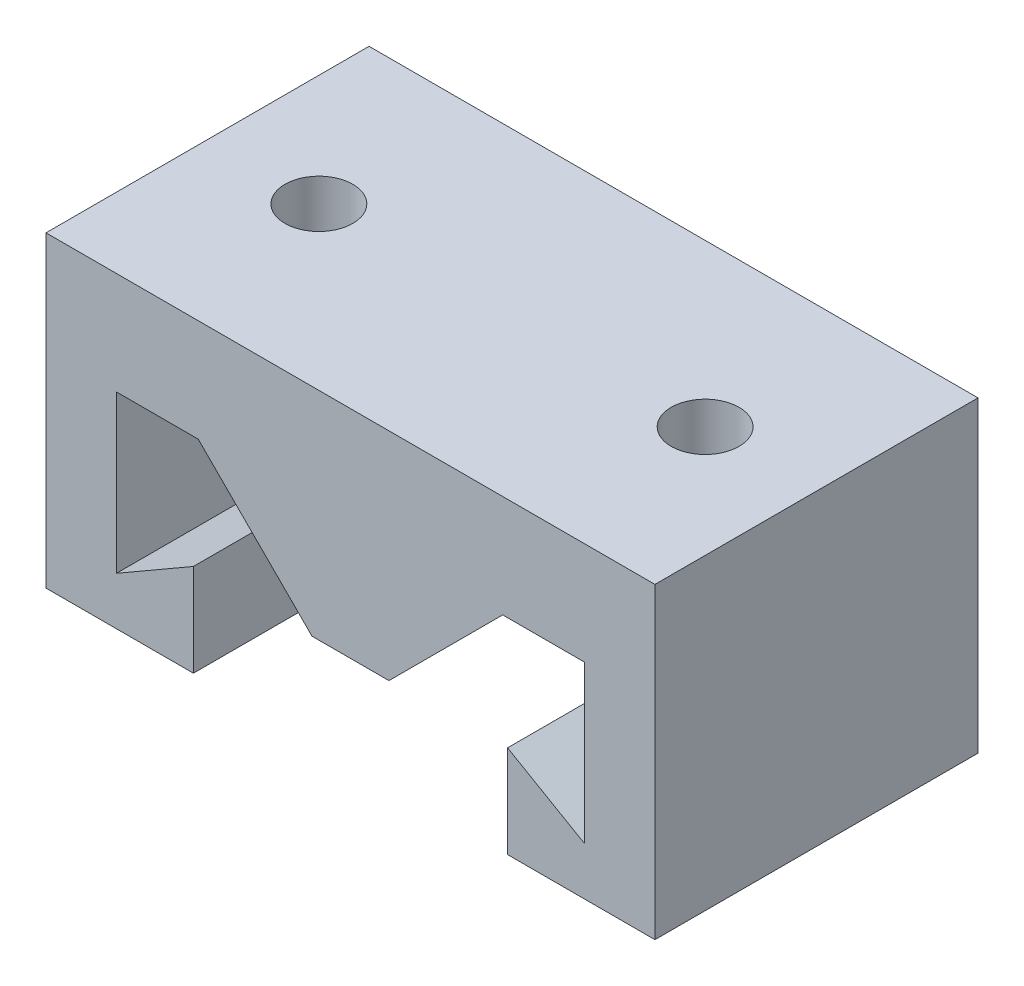
SolidWorks part; units mm, degrees
ref_plane "Front Plane" through (0, 0, 0) normal (0, 0, 1) x (1, 0, 0)
ref_plane "Top Plane" through (0, 0, 0) normal (0, 1, 0) x (1, 0, 0)
ref_plane "Right Plane" through (0, 0, 0) normal (1, 0, 0) x (0, 0, -1)
sketch "Sketch1" plane through (0, 0, 0) normal (0, 0, 1) x (1, 0, 0)
  line L0 (55, 0) -> (-55, 0) construction
  line L1 (-19.05, 0) -> (19.05, 0) construction
  line L2 (-19.05, 0) -> (-19.05, 38.1) construction
  line L3 (-19.05, 38.1) -> (19.05, 38.1) construction
  line L4 (19.05, 0) -> (19.05, 38.1) construction
  line L5 (0, -55) -> (0, 55) construction
  line L6 (9.725, 0) -> (19.05, 0)
  line L7 (19.05, 0) -> (19.05, 19.05)
  line L11 (-19.05, 19.05) -> (-19.05, 0)
  line L12 (-19.05, 0) -> (-9.725, 0)
  line L13 (-9.725, 0) -> (-9.725, 5.7246)
  line L14 (-9.725, 5.7246) -> (-14.4875, 2.975)
  line L15 (-14.4875, 2.975) -> (-14.4875, 12.7)
  line L19 (14.4875, 12.7) -> (14.4875, 2.975)
  line L20 (14.4875, 2.975) -> (9.725, 5.7246)
  line L21 (9.725, 5.7246) -> (9.725, 0)
  line L26 (-14.4875, 12.7) -> (-9.425, 12.7)
  line L28 (-9.425, 12.7) -> (-2.3813, 5.6562)
  line L29 (-2.3813, 5.6562) -> (2.3813, 5.6562)
  line L30 (2.3813, 5.6562) -> (9.425, 12.7)
  line L31 (9.425, 12.7) -> (14.4875, 12.7)
  line L32 (-19.05, 19.05) -> (19.05, 19.05)
  point P6 (0, 0)
  point P24 (0, 5.6562)
  dimension "D1" = 38.1
  dimension "D5" = 4.5625
  dimension "D6" = 4.5625
  dimension "D7" = 9.325
  dimension "D4" = 12.7
  dimension "D2" = 18.85
  dimension "D3" = 45
  dimension "D8" = 60
  dimension "D9" = 9.725
  dimension "D10" = 4.7625
extrude "Boss-Extrude1" add sketch "Sketch1" along normal mid plane 20
sketch "Sketch2" plane through (0, 19.05, 0) normal (0, 1, 0) x (1, 0, 0)
  line L0 (-55, 0) -> (55, 0) construction
  line L1 (-14.4875, 10) -> (-9.425, 10) construction
  line L2 (-14.4875, -10) -> (-9.425, -10) construction
  line L3 (-14.4875, 10) -> (-9.425, 10) construction
  line L4 (-14.4875, -10) -> (-9.425, -10) construction
  line L5 (9.425, 10) -> (14.4875, 10) construction
  line L6 (9.425, -10) -> (14.4875, -10) construction
  line L7 (9.425, 10) -> (14.4875, 10) construction
  line L8 (9.425, -10) -> (14.4875, -10) construction
  line L9 (-11.9563, 10) -> (-11.9563, -10) construction
  line L10 (11.9563, 10) -> (11.9563, -10) construction
  circle A0 centre (-11.9563, 0) radius 2.1
  circle A1 centre (11.9563, 0) radius 2.1
  dimension "D1" = 4.2
extrude "Cut-Extrude1" cut sketch "Sketch2" against normal up to surface (6.35 mm away) up to face at (-11.9563, 12.7, 0)
sketch "Sketch3" plane through (0, 0, 0) normal (0, 0, 1) x (1, 0, 0)
  line L0 (11, 0) -> (-11, 0) construction
  line L1 (-28.575, 0) -> (-18.85, 0)
  line L2 (-28.575, 0) -> (-28.575, 19.05)
  line L3 (-28.575, 19.05) -> (-18.85, 19.05)
  line L4 (-18.85, 0) -> (-18.85, 19.05)
  line L5 (19.05, 19.05) -> (-19.05, 19.05) construction
  line L6 (28.575, 0) -> (18.85, 0)
  line L7 (28.575, 0) -> (28.575, 19.05)
  line L8 (28.575, 19.05) -> (18.85, 19.05)
  line L9 (18.85, 0) -> (18.85, 19.05)
  line L10 (-18.85, 9.525) -> (18.85, 9.525) construction
  line L11 (0, -10.4775) -> (0, 10.4775) construction
  point P14 (0, 9.525)
  dimension "D1" = 57.15
  dimension "D2" = 37.7
extrude "Cut-Extrude2" cut sketch "Sketch3" against normal through all both and the other way through all
equation "\"ViseLength\"= 5in'length of vise in inches"
equation "\"Angle\"= 0'Angle of vise in degrees"
equation "\"ViseWidth\"= 1.5in'width of vise (approximately the scaling factor)"
equation "\"D5@Sketch1\"=\"ViseWidth\"/8-.2"
equation "\"D6@Sketch1\"=\"ViseWidth\"/8-.2"
equation "\"D7@Sketch1\"=\"ViseWidth\"/4-.2"
equation "\"D4@Sketch1\"=\"ViseWidth\"/3"
equation "\"D2@Sketch1\"=\"ViseWidth\"/2-.2"
equation "\"D9@Sketch1\"=\"ViseWidth\"/4+.2"
equation "\"D10@Sketch1\"=\"ViseWidth\"/8"
equation "\"D1@Sketch1\"=\"ViseWidth\""
equation "\"D1@Sketch3\"=\"ViseWidth\"*1.5"
equation "\"D2@Sketch3\"=\"ViseWidth\"-.4"
